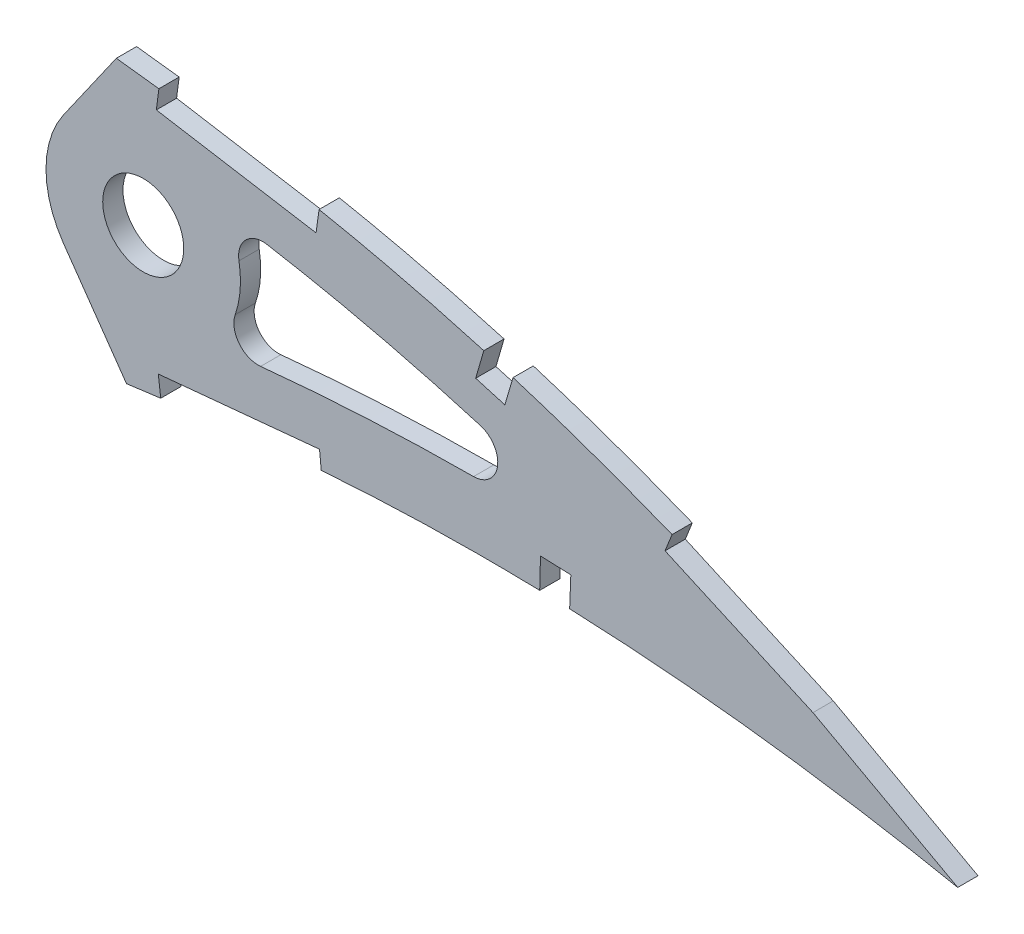
SolidWorks part; units mm, degrees
ref_plane "Front Plane" through (0, 0, 0) normal (0, 0, 1) x (1, 0, 0)
ref_plane "Top Plane" through (0, 0, 0) normal (0, 1, 0) x (1, 0, 0)
ref_plane "Right Plane" through (0, 0, 0) normal (1, 0, 0) x (0, 0, -1)
curve "Curve1"
  spline degree 3 poles (418.0125, 0.6517, 0) (417.9804, 0.6715, 0) (417.8525, 0.7505, 0) (417.5642, 0.9274, 0) (417.084, 1.2219, 0) (416.4119, 1.6322, 0) (415.5483, 2.157, 0) (414.4927, 2.7927, 0) (413.2459, 3.5372, 0) (411.8081, 4.387, 0) (410.1795, 5.3382, 0) (408.3608, 6.3869, 0) (406.352, 7.527, 0) (404.1539, 8.7541, 0) (401.7673, 10.0622, 0) (399.1927, 11.4455, 0) (396.4309, 12.8968, 0) (393.4831, 14.4101, 0) (390.3497, 15.9768, 0) (387.0323, 17.5905, 0) (383.532, 19.2431, 0) (379.8498, 20.9259, 0) (375.9881, 22.6319, 0) (371.9478, 24.3506, 0) (367.7312, 26.0745, 0) (363.3401, 27.7938, 0) (358.7771, 29.5006, 0) (354.0441, 31.184, 0) (349.1444, 32.8365, 0) (344.0806, 34.4474, 0) (338.8562, 36.008, 0) (333.4742, 37.5082, 0) (327.9392, 38.9402, 0) (322.2547, 40.2936, 0) (316.4254, 41.5594, 0) (310.456, 42.7299, 0) (304.3515, 43.7936, 0) (298.1289, 44.7494, 0) (291.8882, 45.5445, 0) (285.6603, 46.3243, 0) (279.4418, 47.0569, 0) (273.1472, 47.7584, 0) (266.7827, 48.425, 0) (260.3545, 49.0544, 0) (253.8692, 49.6441, 0) (247.3335, 50.1923, 0) (240.7538, 50.6959, 0) (234.1369, 51.1541, 0) (227.4895, 51.5628, 0) (220.8185, 51.9218, 0) (214.1308, 52.2286, 0) (207.4334, 52.481, 0) (200.7332, 52.6776, 0) (194.0374, 52.8164, 0) (187.3531, 52.8966, 0) (180.6873, 52.916, 0) (174.0473, 52.8742, 0) (167.44, 52.7698, 0) (160.8726, 52.6014, 0) (154.3521, 52.3686, 0) (147.8856, 52.0716, 0) (141.4801, 51.7078, 0) (135.1426, 51.2797, 0) (128.8802, 50.7853, 0) (122.6997, 50.2246, 0) (116.6076, 49.5999, 0) (110.6107, 48.9095, 0) (104.7154, 48.1553, 0) (98.9282, 47.3389, 0) (93.2555, 46.4598, 0) (87.7035, 45.5205, 0) (82.2781, 44.522, 0) (76.9851, 43.4673, 0) (71.8302, 42.3565, 0) (66.8189, 41.1931, 0) (61.9564, 39.979, 0) (57.2479, 38.7165, 0) (52.6982, 37.4086, 0) (48.3119, 36.0583, 0) (44.0941, 34.667, 0) (40.048, 33.2401, 0) (36.1786, 31.7785, 0) (32.4888, 30.2868, 0) (28.983, 28.767, 0) (25.6637, 27.2237, 0) (22.5348, 25.6586, 0) (19.5984, 24.0762, 0) (16.8576, 22.4789, 0) (14.3149, 20.8697, 0) (11.9714, 19.2526, 0) (9.8303, 17.6287, 0) (7.8925, 16.002, 0) (6.159, 14.375, 0) (4.6325, 12.7489, 0) (3.3127, 11.1265, 0) (2.2016, 9.5091, 0) (1.2991, 7.8983, 0) (0.6075, 6.2951, 0) (0.126, 4.7006, 0) (-0.1376, 3.117, 0) (-0.2032, 1.5431, 0) (-0.0676, 0.5136, 0) (0, 0, 0) knots 0 0 0 0 0.000254 0.001015 0.002283 0.004057 0.006331 0.009105 0.012374 0.016134 0.02038 0.025106 0.030306 0.035972 0.0421 0.048678 0.055702 0.06316 0.071046 0.07935 0.088063 0.097176 0.106678 0.116562 0.126814 0.137428 0.148394 0.1597 0.171338 0.183298 0.19557 0.208144 0.221012 0.234162 0.247587 0.261277 0.275223 0.289414 0.303771 0.317689 0.331784 0.34604 0.360444 0.374983 0.38964 0.404403 0.419257 0.434187 0.449177 0.464215 0.479284 0.49437 0.509458 0.524532 0.539579 0.554583 0.56953 0.584403 0.599191 0.613877 0.628447 0.642889 0.657186 0.671326 0.685294 0.699078 0.712665 0.726043 0.739198 0.752118 0.764792 0.777208 0.789356 0.801224 0.812804 0.824083 0.835055 0.84571 0.856038 0.866034 0.875689 0.884998 0.893953 0.902553 0.910789 0.918661 0.926166 0.933303 0.940071 0.946475 0.952518 0.958205 0.963547 0.968557 0.97325 0.977651 0.981787 0.985694 0.989415 0.993001 0.996508 1 1 1 1
curve "Curve2"
  spline degree 3 poles (0, 0, 0) (0.1073, -0.5067, 0) (0.3225, -1.5225, 0) (0.9071, -2.9849, 0) (1.6803, -4.3906, 0) (2.6581, -5.736, 0) (3.8343, -7.0207, 0) (5.206, -8.246, 0) (6.772, -9.4112, 0) (8.5303, -10.5159, 0) (10.4783, -11.5612, 0) (12.6138, -12.5465, 0) (14.9348, -13.4715, 0) (17.4389, -14.3348, 0) (20.1229, -15.1379, 0) (22.9843, -15.8787, 0) (26.0199, -16.5584, 0) (29.2267, -17.1751, 0) (32.6013, -17.7296, 0) (36.1401, -18.2214, 0) (39.8395, -18.651, 0) (43.6959, -19.0173, 0) (47.7054, -19.3212, 0) (51.8641, -19.5629, 0) (56.168, -19.7432, 0) (60.6128, -19.8613, 0) (65.1943, -19.9191, 0) (69.9083, -19.9175, 0) (74.7502, -19.8561, 0) (79.7159, -19.7382, 0) (84.8006, -19.5631, 0) (89.9997, -19.3329, 0) (95.3085, -19.05, 0) (100.7222, -18.7153, 0) (106.2362, -18.3302, 0) (111.8455, -17.8979, 0) (117.5452, -17.4195, 0) (123.3302, -16.8976, 0) (129.1955, -16.3351, 0) (135.1358, -15.7335, 0) (141.1461, -15.0958, 0) (147.221, -14.4241, 0) (153.3552, -13.7218, 0) (159.5432, -12.9903, 0) (165.7798, -12.2338, 0) (172.059, -11.4536, 0) (178.3757, -10.6529, 0) (184.7241, -9.8353, 0) (191.0984, -9.0009, 0) (197.493, -8.1554, 0) (203.902, -7.2983, 0) (210.3197, -6.4339, 0) (216.7401, -5.5649, 0) (223.157, -4.6917, 0) (229.5648, -3.8177, 0) (235.9575, -2.9455, 0) (242.3289, -2.075, 0) (248.6732, -1.2107, 0) (254.984, -0.3523, 0) (261.2554, 0.4983, 0) (267.4816, 1.3385, 0) (273.6565, 2.1675, 0) (279.7739, 2.9846, 0) (285.8276, 3.7901, 0) (291.7208, 4.5595, 0) (297.4382, 5.334, 0) (302.999, 5.9689, 0) (308.4906, 6.5107, 0) (313.9186, 6.955, 0) (319.2766, 7.3081, 0) (324.5584, 7.5724, 0) (329.7577, 7.7517, 0) (334.868, 7.8514, 0) (339.8828, 7.8739, 0) (344.7953, 7.8264, 0) (349.5992, 7.7127, 0) (354.2877, 7.538, 0) (358.8543, 7.3082, 0) (363.2925, 7.0294, 0) (367.5956, 6.7058, 0) (371.7576, 6.345, 0) (375.7722, 5.9523, 0) (379.6331, 5.5321, 0) (383.3347, 5.0933, 0) (386.8711, 4.6386, 0) (390.237, 4.1757, 0) (393.427, 3.7092, 0) (396.4359, 3.245, 0) (399.2592, 2.7876, 0) (401.8921, 2.3431, 0) (404.3306, 1.9155, 0) (406.5705, 1.5092, 0) (408.6087, 1.1291, 0) (410.4411, 0.7773, 0) (412.0652, 0.4594, 0) (413.4782, 0.1769, 0) (414.6777, -0.0662, 0) (415.6619, -0.269, 0) (416.4292, -0.4281, 0) (416.9781, -0.5438, 0) (417.3079, -0.6126, 0) (417.4545, -0.6439, 0) (417.4911, -0.6517, 0) knots 0 0 0 0 0.003638 0.007293 0.011028 0.014901 0.018963 0.023258 0.027821 0.032679 0.037853 0.043362 0.049215 0.055422 0.061989 0.068918 0.076211 0.083868 0.091887 0.100266 0.109 0.118085 0.127515 0.137285 0.147388 0.157816 0.168563 0.179619 0.190977 0.202627 0.21456 0.226767 0.239236 0.251959 0.264924 0.27812 0.291536 0.30516 0.318981 0.332985 0.347163 0.361499 0.375981 0.390597 0.405333 0.420175 0.43511 0.450124 0.465203 0.480333 0.495501 0.51069 0.525887 0.541078 0.556247 0.571382 0.586466 0.601485 0.616424 0.631269 0.646007 0.660621 0.675098 0.689423 0.703582 0.716908 0.730009 0.742952 0.755726 0.76832 0.780724 0.792927 0.804916 0.816679 0.828204 0.839475 0.850481 0.861208 0.871639 0.881763 0.891564 0.901027 0.910139 0.918884 0.927249 0.935221 0.942785 0.949928 0.956638 0.962904 0.968712 0.974054 0.978918 0.983297 0.98718 0.990561 0.993433 0.995791 0.99763 0.998946 0.999737 1 1 1 1
sketch "Sketch1" plane through (0, 0, 0) normal (0, 0, 1) x (1, 0, 0)
  line L25 (417.4911, -0.6517) -> (421.451, -1.4725)
  line L26 (418.0125, 0.6517) -> (421.451, -1.4725)
  spline S2 degree 3 poles (-2901.6072, -758.8258) (62.2286, 60.9377) (-7.5382, 18.1399) (0.9071, -2.9849) (1.6803, -4.3906) (2.6581, -5.736) (3.8343, -7.0207) (5.206, -8.246) (6.772, -9.4112) (8.5303, -10.5159) (10.4783, -11.5612) (12.6138, -12.5465) (14.9348, -13.4715) (17.4389, -14.3348) (20.1229, -15.1379) (22.9843, -15.8787) (26.0199, -16.5584) (29.2267, -17.1751) (32.6013, -17.7296) (36.1401, -18.2214) (39.8395, -18.651) (43.6959, -19.0173) (47.7054, -19.3212) (51.8641, -19.5629) (56.168, -19.7432) (60.6128, -19.8613) (65.1943, -19.9191) (69.9083, -19.9175) (74.7502, -19.8561) (79.7159, -19.7382) (84.8006, -19.5631) (89.9997, -19.3329) (95.3085, -19.05) (100.7222, -18.7153) (106.2362, -18.3302) (111.8455, -17.8979) (117.5452, -17.4195) (123.3302, -16.8976) (129.1955, -16.3351) (135.1358, -15.7335) (141.1461, -15.0958) (147.221, -14.4241) (153.3552, -13.7218) (159.5432, -12.9903) (165.7798, -12.2338) (172.059, -11.4536) (178.3757, -10.6529) (184.7241, -9.8353) (191.0984, -9.0009) (197.493, -8.1554) (203.902, -7.2983) (210.3197, -6.4339) (216.7401, -5.5649) (223.157, -4.6917) (229.5648, -3.8177) (235.9575, -2.9455) (242.3289, -2.075) (248.6732, -1.2107) (254.984, -0.3523) (261.2554, 0.4983) (267.4816, 1.3385) (273.6565, 2.1675) (279.7739, 2.9846) (285.8276, 3.7901) (291.7208, 4.5595) (297.4382, 5.334) (302.999, 5.9689) (308.4906, 6.5107) (313.9186, 6.955) (319.2766, 7.3081) (324.5584, 7.5724) (329.7577, 7.7517) (334.868, 7.8514) (339.8828, 7.8739) (344.7953, 7.8264) (349.5992, 7.7127) (354.2877, 7.538) (358.8543, 7.3082) (363.2925, 7.0294) (367.5956, 6.7058) (371.7576, 6.345) (375.7722, 5.9523) (379.6331, 5.5321) (383.3347, 5.0933) (386.8711, 4.6386) (390.237, 4.1757) (393.427, 3.7092) (396.4359, 3.245) (399.2592, 2.7876) (401.8921, 2.3431) (404.3306, 1.9155) (406.5705, 1.5092) (408.6087, 1.1291) (410.4411, 0.7773) (412.0652, 0.4594) (413.4782, 0.1769) (414.6777, -0.0662) (415.6619, -0.269) (416.4292, -0.4281) (416.9781, -0.5438) (432.6216, -3.8089) (446.5682, -14.1933) (1083.8628, 2923.4074) knots -0.148283 -0.148283 -0.148283 -0.148283 0.003638 0.007293 0.011028 0.014901 0.018963 0.023258 0.027821 0.032679 0.037853 0.043362 0.049215 0.055422 0.061989 0.068918 0.076211 0.083868 0.091887 0.100266 0.109 0.118085 0.127515 0.137285 0.147388 0.157816 0.168563 0.179619 0.190977 0.202627 0.21456 0.226767 0.239236 0.251959 0.264924 0.27812 0.291536 0.30516 0.318981 0.332985 0.347163 0.361499 0.375981 0.390597 0.405333 0.420175 0.43511 0.450124 0.465203 0.480333 0.495501 0.51069 0.525887 0.541078 0.556247 0.571382 0.586466 0.601485 0.616424 0.631269 0.646007 0.660621 0.675098 0.689423 0.703582 0.716908 0.730009 0.742952 0.755726 0.76832 0.780724 0.792927 0.804916 0.816679 0.828204 0.839475 0.850481 0.861208 0.871639 0.881763 0.891564 0.901027 0.910139 0.918884 0.927249 0.935221 0.942785 0.949928 0.956638 0.962904 0.968712 0.974054 0.978918 0.983297 0.98718 0.990561 0.993433 0.995791 0.99763 0.998946 0.999737 1.110049 1.110049 1.110049 1.110049 only from (0, 0) to (417.4911, -0.6517) construction
  spline S3 degree 3 poles (2035.6651, 2526.3996) (444.3669, -23.2124) (432.7668, -8.3977) (417.5642, 0.9274) (417.084, 1.2219) (416.4119, 1.6322) (415.5483, 2.157) (414.4927, 2.7927) (413.2459, 3.5372) (411.8081, 4.387) (410.1795, 5.3382) (408.3608, 6.3869) (406.352, 7.527) (404.1539, 8.7541) (401.7673, 10.0622) (399.1927, 11.4455) (396.4309, 12.8968) (393.4831, 14.4101) (390.3497, 15.9768) (387.0323, 17.5905) (383.532, 19.2431) (379.8498, 20.9259) (375.9881, 22.6319) (371.9478, 24.3506) (367.7312, 26.0745) (363.3401, 27.7938) (358.7771, 29.5006) (354.0441, 31.184) (349.1444, 32.8365) (344.0806, 34.4474) (338.8562, 36.008) (333.4742, 37.5082) (327.9392, 38.9402) (322.2547, 40.2936) (316.4254, 41.5594) (310.456, 42.7299) (304.3515, 43.7936) (298.1289, 44.7494) (291.8882, 45.5445) (285.6603, 46.3243) (279.4418, 47.0569) (273.1472, 47.7584) (266.7827, 48.425) (260.3545, 49.0544) (253.8692, 49.6441) (247.3335, 50.1923) (240.7538, 50.6959) (234.1369, 51.1541) (227.4895, 51.5628) (220.8185, 51.9218) (214.1308, 52.2286) (207.4334, 52.481) (200.7332, 52.6776) (194.0374, 52.8164) (187.3531, 52.8966) (180.6873, 52.916) (174.0473, 52.8742) (167.44, 52.7698) (160.8726, 52.6014) (154.3521, 52.3686) (147.8856, 52.0716) (141.4801, 51.7078) (135.1426, 51.2797) (128.8802, 50.7853) (122.6997, 50.2246) (116.6076, 49.5999) (110.6107, 48.9095) (104.7154, 48.1553) (98.9282, 47.3389) (93.2555, 46.4598) (87.7035, 45.5205) (82.2781, 44.522) (76.9851, 43.4673) (71.8302, 42.3565) (66.8189, 41.1931) (61.9564, 39.979) (57.2479, 38.7165) (52.6982, 37.4086) (48.3119, 36.0583) (44.0941, 34.667) (40.048, 33.2401) (36.1786, 31.7785) (32.4888, 30.2868) (28.983, 28.767) (25.6637, 27.2237) (22.5348, 25.6586) (19.5984, 24.0762) (16.8576, 22.4789) (14.3149, 20.8697) (11.9714, 19.2526) (9.8303, 17.6287) (7.8925, 16.002) (6.159, 14.375) (4.6325, 12.7489) (3.3127, 11.1265) (2.2016, 9.5091) (1.2991, 7.8983) (0.6075, 6.2951) (0.126, 4.7006) (-0.1376, 3.117) (-1.0834, -19.5745) (79.1081, -36.6721) (-2988.5065, -249.641) knots -0.11811 -0.11811 -0.11811 -0.11811 0.000254 0.001015 0.002283 0.004057 0.006331 0.009105 0.012374 0.016134 0.02038 0.025106 0.030306 0.035972 0.0421 0.048678 0.055702 0.06316 0.071046 0.07935 0.088063 0.097176 0.106678 0.116562 0.126814 0.137428 0.148394 0.1597 0.171338 0.183298 0.19557 0.208144 0.221012 0.234162 0.247587 0.261277 0.275223 0.289414 0.303771 0.317689 0.331784 0.34604 0.360444 0.374983 0.38964 0.404403 0.419257 0.434187 0.449177 0.464215 0.479284 0.49437 0.509458 0.524532 0.539579 0.554583 0.56953 0.584403 0.599191 0.613877 0.628447 0.642889 0.657186 0.671326 0.685294 0.699078 0.712665 0.726043 0.739198 0.752118 0.764792 0.777208 0.789356 0.801224 0.812804 0.824083 0.835055 0.84571 0.856038 0.866034 0.875689 0.884998 0.893953 0.902553 0.910789 0.918661 0.926166 0.933303 0.940071 0.946475 0.952518 0.958205 0.963547 0.968557 0.97325 0.977651 0.981787 0.985694 0.989415 0.993001 0.996508 1.142022 1.142022 1.142022 1.142022 only from (418.0125, 0.6517) to (0, 0) construction
  spline S4 degree 3 poles (0, 0) (0.1073, -0.5067) (0.3225, -1.5225) (0.9071, -2.9849) (1.6803, -4.3906) (2.6581, -5.736) (3.8343, -7.0207) (5.206, -8.246) (6.772, -9.4112) (8.5303, -10.5159) (10.4783, -11.5612) (12.6138, -12.5465) (14.9348, -13.4715) (17.4389, -14.3348) (20.1229, -15.1379) (22.9843, -15.8787) (26.0199, -16.5584) (29.2267, -17.1751) (32.6013, -17.7296) (36.1401, -18.2214) (39.8395, -18.651) (43.6959, -19.0173) (47.7054, -19.3212) (51.8641, -19.5629) (56.168, -19.7432) (60.6128, -19.8613) (65.1943, -19.9191) (69.9083, -19.9175) (74.7502, -19.8561) (79.7159, -19.7382) (84.8006, -19.5631) (89.9997, -19.3329) (95.3085, -19.05) (100.7222, -18.7153) (106.2362, -18.3302) (111.8455, -17.8979) (117.5452, -17.4195) (123.3302, -16.8976) (129.1955, -16.3351) (135.1358, -15.7335) (141.1461, -15.0958) (147.221, -14.4241) (153.3552, -13.7218) (159.5432, -12.9903) (165.7798, -12.2338) (172.059, -11.4536) (178.3757, -10.6529) (184.7241, -9.8353) (191.0984, -9.0009) (197.493, -8.1554) (203.902, -7.2983) (210.3197, -6.4339) (216.7401, -5.5649) (223.157, -4.6917) (229.5648, -3.8177) (235.9575, -2.9455) (242.3289, -2.075) (248.6732, -1.2107) (254.984, -0.3523) (261.2554, 0.4983) (267.4816, 1.3385) (273.6565, 2.1675) (279.7739, 2.9846) (285.8276, 3.7901) (291.7208, 4.5595) (297.4382, 5.334) (302.999, 5.9689) (308.4906, 6.5107) (313.9186, 6.955) (319.2766, 7.3081) (324.5584, 7.5724) (329.7577, 7.7517) (334.868, 7.8514) (339.8828, 7.8739) (344.7953, 7.8264) (349.5992, 7.7127) (354.2877, 7.538) (358.8543, 7.3082) (363.2925, 7.0294) (367.5956, 6.7058) (371.7576, 6.345) (375.7722, 5.9523) (379.6331, 5.5321) (383.3347, 5.0933) (386.8711, 4.6386) (390.237, 4.1757) (393.427, 3.7092) (396.4359, 3.245) (399.2592, 2.7876) (401.8921, 2.3431) (404.3306, 1.9155) (406.5705, 1.5092) (408.6087, 1.1291) (410.4411, 0.7773) (412.0652, 0.4594) (413.4782, 0.1769) (414.6777, -0.0662) (415.6619, -0.269) (416.4292, -0.4281) (416.9781, -0.5438) (417.3079, -0.6126) (417.4545, -0.6439) (417.4911, -0.6517) knots 0 0 0 0 0.003638 0.007293 0.011028 0.014901 0.018963 0.023258 0.027821 0.032679 0.037853 0.043362 0.049215 0.055422 0.061989 0.068918 0.076211 0.083868 0.091887 0.100266 0.109 0.118085 0.127515 0.137285 0.147388 0.157816 0.168563 0.179619 0.190977 0.202627 0.21456 0.226767 0.239236 0.251959 0.264924 0.27812 0.291536 0.30516 0.318981 0.332985 0.347163 0.361499 0.375981 0.390597 0.405333 0.420175 0.43511 0.450124 0.465203 0.480333 0.495501 0.51069 0.525887 0.541078 0.556247 0.571382 0.586466 0.601485 0.616424 0.631269 0.646007 0.660621 0.675098 0.689423 0.703582 0.716908 0.730009 0.742952 0.755726 0.76832 0.780724 0.792927 0.804916 0.816679 0.828204 0.839475 0.850481 0.861208 0.871639 0.881763 0.891564 0.901027 0.910139 0.918884 0.927249 0.935221 0.942785 0.949928 0.956638 0.962904 0.968712 0.974054 0.978918 0.983297 0.98718 0.990561 0.993433 0.995791 0.99763 0.998946 0.999737 1 1 1 1
  spline S5 degree 3 poles (418.0125, 0.6517) (417.9804, 0.6715) (417.8525, 0.7505) (417.5642, 0.9274) (417.084, 1.2219) (416.4119, 1.6322) (415.5483, 2.157) (414.4927, 2.7927) (413.2459, 3.5372) (411.8081, 4.387) (410.1795, 5.3382) (408.3608, 6.3869) (406.352, 7.527) (404.1539, 8.7541) (401.7673, 10.0622) (399.1927, 11.4455) (396.4309, 12.8968) (393.4831, 14.4101) (390.3497, 15.9768) (387.0323, 17.5905) (383.532, 19.2431) (379.8498, 20.9259) (375.9881, 22.6319) (371.9478, 24.3506) (367.7312, 26.0745) (363.3401, 27.7938) (358.7771, 29.5006) (354.0441, 31.184) (349.1444, 32.8365) (344.0806, 34.4474) (338.8562, 36.008) (333.4742, 37.5082) (327.9392, 38.9402) (322.2547, 40.2936) (316.4254, 41.5594) (310.456, 42.7299) (304.3515, 43.7936) (298.1289, 44.7494) (291.8882, 45.5445) (285.6603, 46.3243) (279.4418, 47.0569) (273.1472, 47.7584) (266.7827, 48.425) (260.3545, 49.0544) (253.8692, 49.6441) (247.3335, 50.1923) (240.7538, 50.6959) (234.1369, 51.1541) (227.4895, 51.5628) (220.8185, 51.9218) (214.1308, 52.2286) (207.4334, 52.481) (200.7332, 52.6776) (194.0374, 52.8164) (187.3531, 52.8966) (180.6873, 52.916) (174.0473, 52.8742) (167.44, 52.7698) (160.8726, 52.6014) (154.3521, 52.3686) (147.8856, 52.0716) (141.4801, 51.7078) (135.1426, 51.2797) (128.8802, 50.7853) (122.6997, 50.2246) (116.6076, 49.5999) (110.6107, 48.9095) (104.7154, 48.1553) (98.9282, 47.3389) (93.2555, 46.4598) (87.7035, 45.5205) (82.2781, 44.522) (76.9851, 43.4673) (71.8302, 42.3565) (66.8189, 41.1931) (61.9564, 39.979) (57.2479, 38.7165) (52.6982, 37.4086) (48.3119, 36.0583) (44.0941, 34.667) (40.048, 33.2401) (36.1786, 31.7785) (32.4888, 30.2868) (28.983, 28.767) (25.6637, 27.2237) (22.5348, 25.6586) (19.5984, 24.0762) (16.8576, 22.4789) (14.3149, 20.8697) (11.9714, 19.2526) (9.8303, 17.6287) (7.8925, 16.002) (6.159, 14.375) (4.6325, 12.7489) (3.3127, 11.1265) (2.2016, 9.5091) (1.2991, 7.8983) (0.6075, 6.2951) (0.126, 4.7006) (-0.1376, 3.117) (-0.2032, 1.5431) (-0.0676, 0.5136) (0, 0) knots 0 0 0 0 0.000254 0.001015 0.002283 0.004057 0.006331 0.009105 0.012374 0.016134 0.02038 0.025106 0.030306 0.035972 0.0421 0.048678 0.055702 0.06316 0.071046 0.07935 0.088063 0.097176 0.106678 0.116562 0.126814 0.137428 0.148394 0.1597 0.171338 0.183298 0.19557 0.208144 0.221012 0.234162 0.247587 0.261277 0.275223 0.289414 0.303771 0.317689 0.331784 0.34604 0.360444 0.374983 0.38964 0.404403 0.419257 0.434187 0.449177 0.464215 0.479284 0.49437 0.509458 0.524532 0.539579 0.554583 0.56953 0.584403 0.599191 0.613877 0.628447 0.642889 0.657186 0.671326 0.685294 0.699078 0.712665 0.726043 0.739198 0.752118 0.764792 0.777208 0.789356 0.801224 0.812804 0.824083 0.835055 0.84571 0.856038 0.866034 0.875689 0.884998 0.893953 0.902553 0.910789 0.918661 0.926166 0.933303 0.940071 0.946475 0.952518 0.958205 0.963547 0.968557 0.97325 0.977651 0.981787 0.985694 0.989415 0.993001 0.996508 1 1 1 1
extrude "Boss-Extrude1" add sketch "Sketch1" along normal blind 3.175
sketch "Sketch3" plane through (0, 0, 0) normal (0, 0, -1) x (-1, 0, 0)
  circle A1 centre (-285.7292, 26.2554) radius 6.35
extrude "Cut-Extrude2" cut sketch "Sketch3" against normal blind 7.62
sketch "Sketch4" plane through (0, 0, 3.175) normal (0, 0, 1) x (1, 0, 0)
  line L0 (273.2453, 34.9967) -> (281.5171, 46.8101)
  line L1 (273.2453, 17.5141) -> (283.1086, 3.4278)
  line L2 (285.7292, 26.2554) -> (311.044, 26.2554)
  circle A0 centre (285.7292, 26.2554) radius 6.35 construction
  circle A1 centre (285.7292, 26.2554) radius 6.35
  circle A2 centre (285.7292, 26.2554) radius 15.24
  spline S0 degree 3 poles (-1937.7253, -493.2296) (46.5589, 50.9528) (-6.5452, 15.6559) (0.9071, -2.9849) (1.6803, -4.3906) (2.6581, -5.736) (3.8343, -7.0207) (5.206, -8.246) (6.772, -9.4112) (8.5303, -10.5159) (10.4783, -11.5612) (12.6138, -12.5465) (14.9348, -13.4715) (17.4389, -14.3348) (20.1229, -15.1379) (22.9843, -15.8787) (26.0199, -16.5584) (29.2267, -17.1751) (32.6013, -17.7296) (36.1401, -18.2214) (39.8395, -18.651) (43.6959, -19.0173) (47.7054, -19.3212) (51.8641, -19.5629) (56.168, -19.7432) (60.6128, -19.8613) (65.1943, -19.9191) (69.9083, -19.9175) (74.7502, -19.8561) (79.7159, -19.7382) (84.8006, -19.5631) (89.9997, -19.3329) (95.3085, -19.05) (100.7222, -18.7153) (106.2362, -18.3302) (111.8455, -17.8979) (117.5452, -17.4195) (123.3302, -16.8976) (129.1955, -16.3351) (135.1358, -15.7335) (141.1461, -15.0958) (147.221, -14.4241) (153.3552, -13.7218) (159.5432, -12.9903) (165.7798, -12.2338) (172.059, -11.4536) (178.3757, -10.6529) (184.7241, -9.8353) (191.0984, -9.0009) (197.493, -8.1554) (203.902, -7.2983) (210.3197, -6.4339) (216.7401, -5.5649) (223.157, -4.6917) (229.5648, -3.8177) (235.9575, -2.9455) (242.3289, -2.075) (248.6732, -1.2107) (254.984, -0.3523) (261.2554, 0.4983) (267.4816, 1.3385) (273.6565, 2.1675) (279.7739, 2.9846) (285.8276, 3.7901) (291.7208, 4.5595) (297.4382, 5.334) (302.999, 5.9689) (308.4906, 6.5107) (313.9186, 6.955) (319.2766, 7.3081) (324.5584, 7.5724) (329.7577, 7.7517) (334.868, 7.8514) (339.8828, 7.8739) (344.7953, 7.8264) (349.5992, 7.7127) (354.2877, 7.538) (358.8543, 7.3082) (363.2925, 7.0294) (367.5956, 6.7058) (371.7576, 6.345) (375.7722, 5.9523) (379.6331, 5.5321) (383.3347, 5.0933) (386.8711, 4.6386) (390.237, 4.1757) (393.427, 3.7092) (396.4359, 3.245) (399.2592, 2.7876) (401.8921, 2.3431) (404.3306, 1.9155) (406.5705, 1.5092) (408.6087, 1.1291) (410.4411, 0.7773) (412.0652, 0.4594) (413.4782, 0.1769) (414.6777, -0.0662) (415.6619, -0.269) (416.4292, -0.4281) (416.9781, -0.5438) (430.6853, -3.4047) (443.0511, -11.7044) (871.2046, 1946.5522) knots -0.129551 -0.129551 -0.129551 -0.129551 0.003638 0.007293 0.011028 0.014901 0.018963 0.023258 0.027821 0.032679 0.037853 0.043362 0.049215 0.055422 0.061989 0.068918 0.076211 0.083868 0.091887 0.100266 0.109 0.118085 0.127515 0.137285 0.147388 0.157816 0.168563 0.179619 0.190977 0.202627 0.21456 0.226767 0.239236 0.251959 0.264924 0.27812 0.291536 0.30516 0.318981 0.332985 0.347163 0.361499 0.375981 0.390597 0.405333 0.420175 0.43511 0.450124 0.465203 0.480333 0.495501 0.51069 0.525887 0.541078 0.556247 0.571382 0.586466 0.601485 0.616424 0.631269 0.646007 0.660621 0.675098 0.689423 0.703582 0.716908 0.730009 0.742952 0.755726 0.76832 0.780724 0.792927 0.804916 0.816679 0.828204 0.839475 0.850481 0.861208 0.871639 0.881763 0.891564 0.901027 0.910139 0.918884 0.927249 0.935221 0.942785 0.949928 0.956638 0.962904 0.968712 0.974054 0.978918 0.983297 0.98718 0.990561 0.993433 0.995791 0.99763 0.998946 0.999737 1.096134 1.096134 1.096134 1.096134 only from (0, 0) to (417.4911, -0.6517) construction
  spline S1 degree 3 poles (1505.5404, 1678.541) (441.4039, -19.5852) (430.8807, -7.2408) (417.5642, 0.9274) (417.084, 1.2219) (416.4119, 1.6322) (415.5483, 2.157) (414.4927, 2.7927) (413.2459, 3.5372) (411.8081, 4.387) (410.1795, 5.3382) (408.3608, 6.3869) (406.352, 7.527) (404.1539, 8.7541) (401.7673, 10.0622) (399.1927, 11.4455) (396.4309, 12.8968) (393.4831, 14.4101) (390.3497, 15.9768) (387.0323, 17.5905) (383.532, 19.2431) (379.8498, 20.9259) (375.9881, 22.6319) (371.9478, 24.3506) (367.7312, 26.0745) (363.3401, 27.7938) (358.7771, 29.5006) (354.0441, 31.184) (349.1444, 32.8365) (344.0806, 34.4474) (338.8562, 36.008) (333.4742, 37.5082) (327.9392, 38.9402) (322.2547, 40.2936) (316.4254, 41.5594) (310.456, 42.7299) (304.3515, 43.7936) (298.1289, 44.7494) (291.8882, 45.5445) (285.6603, 46.3243) (279.4418, 47.0569) (273.1472, 47.7584) (266.7827, 48.425) (260.3545, 49.0544) (253.8692, 49.6441) (247.3335, 50.1923) (240.7538, 50.6959) (234.1369, 51.1541) (227.4895, 51.5628) (220.8185, 51.9218) (214.1308, 52.2286) (207.4334, 52.481) (200.7332, 52.6776) (194.0374, 52.8164) (187.3531, 52.8966) (180.6873, 52.916) (174.0473, 52.8742) (167.44, 52.7698) (160.8726, 52.6014) (154.3521, 52.3686) (147.8856, 52.0716) (141.4801, 51.7078) (135.1426, 51.2797) (128.8802, 50.7853) (122.6997, 50.2246) (116.6076, 49.5999) (110.6107, 48.9095) (104.7154, 48.1553) (98.9282, 47.3389) (93.2555, 46.4598) (87.7035, 45.5205) (82.2781, 44.522) (76.9851, 43.4673) (71.8302, 42.3565) (66.8189, 41.1931) (61.9564, 39.979) (57.2479, 38.7165) (52.6982, 37.4086) (48.3119, 36.0583) (44.0941, 34.667) (40.048, 33.2401) (36.1786, 31.7785) (32.4888, 30.2868) (28.983, 28.767) (25.6637, 27.2237) (22.5348, 25.6586) (19.5984, 24.0762) (16.8576, 22.4789) (14.3149, 20.8697) (11.9714, 19.2526) (9.8303, 17.6287) (7.8925, 16.002) (6.159, 14.375) (4.6325, 12.7489) (3.3127, 11.1265) (2.2016, 9.5091) (1.2991, 7.8983) (0.6075, 6.2951) (0.126, 4.7006) (-0.1376, 3.117) (-0.9722, -16.9072) (60.9773, -32.4825) (-1991.3982, -179.4503) knots -0.103174 -0.103174 -0.103174 -0.103174 0.000254 0.001015 0.002283 0.004057 0.006331 0.009105 0.012374 0.016134 0.02038 0.025106 0.030306 0.035972 0.0421 0.048678 0.055702 0.06316 0.071046 0.07935 0.088063 0.097176 0.106678 0.116562 0.126814 0.137428 0.148394 0.1597 0.171338 0.183298 0.19557 0.208144 0.221012 0.234162 0.247587 0.261277 0.275223 0.289414 0.303771 0.317689 0.331784 0.34604 0.360444 0.374983 0.38964 0.404403 0.419257 0.434187 0.449177 0.464215 0.479284 0.49437 0.509458 0.524532 0.539579 0.554583 0.56953 0.584403 0.599191 0.613877 0.628447 0.642889 0.657186 0.671326 0.685294 0.699078 0.712665 0.726043 0.739198 0.752118 0.764792 0.777208 0.789356 0.801224 0.812804 0.824083 0.835055 0.84571 0.856038 0.866034 0.875689 0.884998 0.893953 0.902553 0.910789 0.918661 0.926166 0.933303 0.940071 0.946475 0.952518 0.958205 0.963547 0.968557 0.97325 0.977651 0.981787 0.985694 0.989415 0.993001 0.996508 1.124083 1.124083 1.124083 1.124083 only from (418.0125, 0.6517) to (0, 0) construction
  spline S2 degree 3 poles (180.4181, -10.3891) (181.8505, -10.2052) (185.4085, -9.7457) (191.0984, -9.0009) (197.493, -8.1554) (203.902, -7.2983) (210.3197, -6.4339) (216.7401, -5.5649) (223.157, -4.6917) (229.5648, -3.8177) (235.9575, -2.9455) (242.3289, -2.075) (248.6732, -1.2107) (254.984, -0.3523) (261.2554, 0.4983) (267.4816, 1.3385) (273.6565, 2.1675) (279.7739, 2.9846) (285.8276, 3.7901) (291.7208, 4.5595) (297.4382, 5.334) (302.999, 5.9689) (308.4906, 6.5107) (313.9186, 6.955) (319.2766, 7.3081) (324.5584, 7.5724) (329.7577, 7.7517) (334.868, 7.8514) (339.8828, 7.8739) (344.7953, 7.8264) (349.5992, 7.7127) (354.2877, 7.538) (358.8543, 7.3082) (363.2925, 7.0294) (367.5956, 6.7058) (371.7576, 6.345) (375.7722, 5.9523) (379.6331, 5.5321) (383.3347, 5.0933) (386.8711, 4.6386) (390.237, 4.1757) (393.427, 3.7092) (396.4359, 3.245) (399.2592, 2.7876) (401.8921, 2.3431) (404.3306, 1.9155) (406.5705, 1.5092) (408.6087, 1.1291) (410.4411, 0.7773) (412.0652, 0.4594) (413.4782, 0.1769) (414.6777, -0.0662) (415.6619, -0.269) (416.4292, -0.4281) (416.9781, -0.5438) (417.3079, -0.6126) (417.4545, -0.6439) (417.4911, -0.6517) knots 0.439965 0.439965 0.439965 0.439965 0.450124 0.465203 0.480333 0.495501 0.51069 0.525887 0.541078 0.556247 0.571382 0.586466 0.601485 0.616424 0.631269 0.646007 0.660621 0.675098 0.689423 0.703582 0.716908 0.730009 0.742952 0.755726 0.76832 0.780724 0.792927 0.804916 0.816679 0.828204 0.839475 0.850481 0.861208 0.871639 0.881763 0.891564 0.901027 0.910139 0.918884 0.927249 0.935221 0.942785 0.949928 0.956638 0.962904 0.968712 0.974054 0.978918 0.983297 0.98718 0.990561 0.993433 0.995791 0.99763 0.998946 0.999737 1 1 1 1
  spline S3 degree 3 poles (418.0125, 0.6517) (417.9804, 0.6715) (417.8525, 0.7505) (417.5642, 0.9274) (417.084, 1.2219) (416.4119, 1.6322) (415.5483, 2.157) (414.4927, 2.7927) (413.2459, 3.5372) (411.8081, 4.387) (410.1795, 5.3382) (408.3608, 6.3869) (406.352, 7.527) (404.1539, 8.7541) (401.7673, 10.0622) (399.1927, 11.4455) (396.4309, 12.8968) (393.4831, 14.4101) (390.3497, 15.9768) (387.0323, 17.5905) (383.532, 19.2431) (379.8498, 20.9259) (375.9881, 22.6319) (371.9478, 24.3506) (367.7312, 26.0745) (363.3401, 27.7938) (358.7771, 29.5006) (354.0441, 31.184) (349.1444, 32.8365) (344.0806, 34.4474) (338.8562, 36.008) (333.4742, 37.5082) (327.9392, 38.9402) (322.2547, 40.2936) (316.4254, 41.5594) (310.456, 42.7299) (304.3515, 43.7936) (298.1289, 44.7494) (291.8882, 45.5445) (285.6603, 46.3243) (279.4418, 47.0569) (273.1472, 47.7584) (266.7827, 48.425) (260.3545, 49.0544) (253.8692, 49.6441) (247.3335, 50.1923) (240.7538, 50.6959) (234.1369, 51.1541) (227.4895, 51.5628) (220.8185, 51.9218) (214.1308, 52.2286) (207.4334, 52.481) (200.7332, 52.6776) (194.0374, 52.8164) (187.3531, 52.8966) (180.6873, 52.916) (174.0473, 52.8742) (167.44, 52.7698) (160.8726, 52.6014) (155.4817, 52.4089) (152.281, 52.2704) (151.2539, 52.2234) knots 0 0 0 0 0.000254 0.001015 0.002283 0.004057 0.006331 0.009105 0.012374 0.016134 0.02038 0.025106 0.030306 0.035972 0.0421 0.048678 0.055702 0.06316 0.071046 0.07935 0.088063 0.097176 0.106678 0.116562 0.126814 0.137428 0.148394 0.1597 0.171338 0.183298 0.19557 0.208144 0.221012 0.234162 0.247587 0.261277 0.275223 0.289414 0.303771 0.317689 0.331784 0.34604 0.360444 0.374983 0.38964 0.404403 0.419257 0.434187 0.449177 0.464215 0.479284 0.49437 0.509458 0.524532 0.539579 0.554583 0.56953 0.584403 0.599191 0.613877 0.620817 0.620817 0.620817 0.620817
  spline S4 degree 1 poles (412.6728, -7.992) (151.7184, 42.0741) knots 0 0 1 1 construction
  spline S5 degree 3 poles (412.6728, -7.992) (412.529, -7.9032) (412.2464, -7.7298) (411.6377, -7.3565) (410.5993, -6.7234) (408.5143, -5.4652) (404.306, -2.9803) (395.8163, 1.8196) (378.4768, 10.7592) (357.9235, 19.3569) (336.7625, 26.1844) (323.3258, 29.6855) (312.4652, 32.0171) (305.6501, 33.2719) (300.1537, 34.1638) (296.076, 34.7616) (291.9086, 35.3008) (286.2081, 36.0188) (279.1798, 36.867) (267.8599, 38.1235) (253.7183, 39.5037) (236.7158, 40.8444) (214.0351, 42.1902) (185.6608, 43.0017) (163.0284, 42.5917) (151.7184, 42.0741) knots 0 0 0 0 0.001213 0.002425 0.00485 0.0097 0.019401 0.038801 0.077602 0.155204 0.194005 0.232807 0.252207 0.271608 0.281308 0.291008 0.300708 0.310409 0.329809 0.34921 0.388011 0.426812 0.465613 0.543215 0.620817 0.620817 0.620817 0.620817
  spline S6 degree 1 poles (179.1239, -0.3119) (419.6107, 9.2848) knots 0 0 1 1 construction
  spline S7 degree 3 poles (179.1239, -0.3119) (188.9725, 0.9529) (208.644, 3.5759) (233.2881, 6.9462) (253.0144, 9.6358) (267.829, 11.6393) (278.9188, 13.1245) (286.3557, 14.1051) (290.0348, 14.5872) (293.7202, 15.0843) (297.5682, 15.5751) (301.3934, 16.0072) (306.4806, 16.5301) (315.4288, 17.2991) (328.2209, 17.9712) (343.5941, 18.1039) (364.063, 17.4008) (384.4368, 15.4184) (402.073, 12.6709) (410.8627, 11.0539) (415.2186, 10.1932) (417.2602, 9.7755) (418.1832, 9.5844) (418.673, 9.4822) (419.1054, 9.3912) (419.4468, 9.3197) (419.6107, 9.2848) knots 0.439965 0.439965 0.439965 0.439965 0.50997 0.579974 0.614976 0.649978 0.684981 0.693731 0.702482 0.711232 0.719983 0.728733 0.737484 0.754985 0.789987 0.824989 0.859991 0.929996 0.964998 0.982499 0.991249 0.995625 0.996719 0.997812 0.998906 1 1 1 1
  dimension "D2" = 30.48
  dimension "D1" = 10.16
  dimension "D3" = 55
  dimension "D4" = 55
extrude "Cut-Extrude3" cut sketch "Sketch4" against normal through all
sketch "Sketch5" plane through (0, 0, 3.175) normal (0, 0, 1) x (1, 0, 0)
  line L0 (313.2552, 41.8987) -> (288.194, 46.0769)
  line L1 (313.2552, 41.8987) -> (288.194, 46.0769)
  line L2 (288.194, 46.0769) -> (287.7828, 42.9291)
  line L3 (288.194, 46.0769) -> (287.7828, 42.9291)
  line L4 (313.3657, 9.6572) -> (288.0908, 7.2303)
  line L5 (313.3657, 9.6572) -> (288.0908, 7.2303)
  line L6 (288.0908, 7.2303) -> (288.4802, 4.0794)
  line L7 (288.0908, 7.2303) -> (288.4802, 4.0794)
  line L8 (343.7526, 34.7378) -> (339.168, 36.1061)
  line L9 (343.7526, 34.7378) -> (339.168, 36.1061)
  line L10 (339.168, 36.1061) -> (337.8421, 31.5325)
  line L11 (339.168, 36.1061) -> (337.8421, 31.5325)
  line L12 (352.7568, 12.3038) -> (347.9988, 12.4911)
  line L13 (352.7568, 12.3038) -> (347.9988, 12.4911)
  line L14 (347.9988, 12.4911) -> (347.8753, 7.7308)
  line L15 (347.9988, 12.4911) -> (347.8753, 7.7308)
  line L16 (391.886, 15.5301) -> (368.7011, 25.8958)
  line L17 (391.886, 15.5301) -> (368.7011, 25.8958)
  line L18 (368.7011, 25.8958) -> (367.5249, 22.9474)
  line L19 (368.7011, 25.8958) -> (367.5249, 22.9474)
  line L20 (414.5246, 3.1973) -> (392.2313, 15.3684)
  line L21 (414.5246, 3.1973) -> (392.2313, 15.3684)
  line L22 (413.0032, 0.4106) -> (414.5246, 3.1973)
  line L23 (413.0032, 0.4106) -> (414.5246, 3.1973)
  line L24 (390.7099, 12.5817) -> (413.0032, 0.4106)
  line L25 (390.7099, 12.5817) -> (413.0032, 0.4106)
  line L26 (367.5249, 22.9474) -> (390.7099, 12.5817)
  line L27 (367.5249, 22.9474) -> (390.7099, 12.5817)
  line L28 (352.5709, 7.5776) -> (352.7568, 12.3038)
  line L29 (352.5709, 7.5776) -> (352.7568, 12.3038)
  line L30 (347.8753, 7.7308) -> (352.5709, 7.5776)
  line L31 (347.8753, 7.7308) -> (352.5709, 7.5776)
  line L32 (342.4157, 30.2065) -> (343.7526, 34.7378)
  line L33 (342.4157, 30.2065) -> (343.7526, 34.7378)
  line L34 (337.8421, 31.5325) -> (342.4157, 30.2065)
  line L35 (337.8421, 31.5325) -> (342.4157, 30.2065)
  line L36 (287.7828, 42.9291) -> (312.8213, 38.7536)
  line L37 (287.7828, 42.9291) -> (312.8213, 38.7536)
  line L38 (312.8213, 38.7536) -> (313.2552, 41.8987)
  line L39 (312.8213, 38.7536) -> (313.2552, 41.8987)
  line L40 (313.6697, 6.4979) -> (313.3657, 9.6572)
  line L41 (313.6697, 6.4979) -> (313.3657, 9.6572)
  line L42 (288.4802, 4.0794) -> (313.6697, 6.4979)
  line L43 (288.4802, 4.0794) -> (313.6697, 6.4979)
  line L44 (288.194, 46.0769) -> (288.7888, 50.3891)
  line L45 (313.2552, 41.8987) -> (313.8742, 46.386)
  line L46 (368.7011, 25.8958) -> (370.4349, 29.7738)
  line L47 (370.4349, 29.7738) -> (442.5317, 29.7738)
  line L48 (442.5317, 29.7738) -> (442.5317, -15.7106)
  line L49 (442.5317, -15.7106) -> (413.0032, 0.4106)
  line L50 (347.8753, 7.7308) -> (347.7745, 3.8459)
  line L51 (352.5709, 7.5776) -> (352.4057, 3.3777)
extrude "Cut-Extrude7" cut sketch "Sketch5" against normal through all
fillet "Fillet1" radius 3.81 3 edges at (362.3528, 17.2653, 1.5875) (298.6195, 34.3854, 1.5875) (296.4559, 15.4298, 1.5875)
